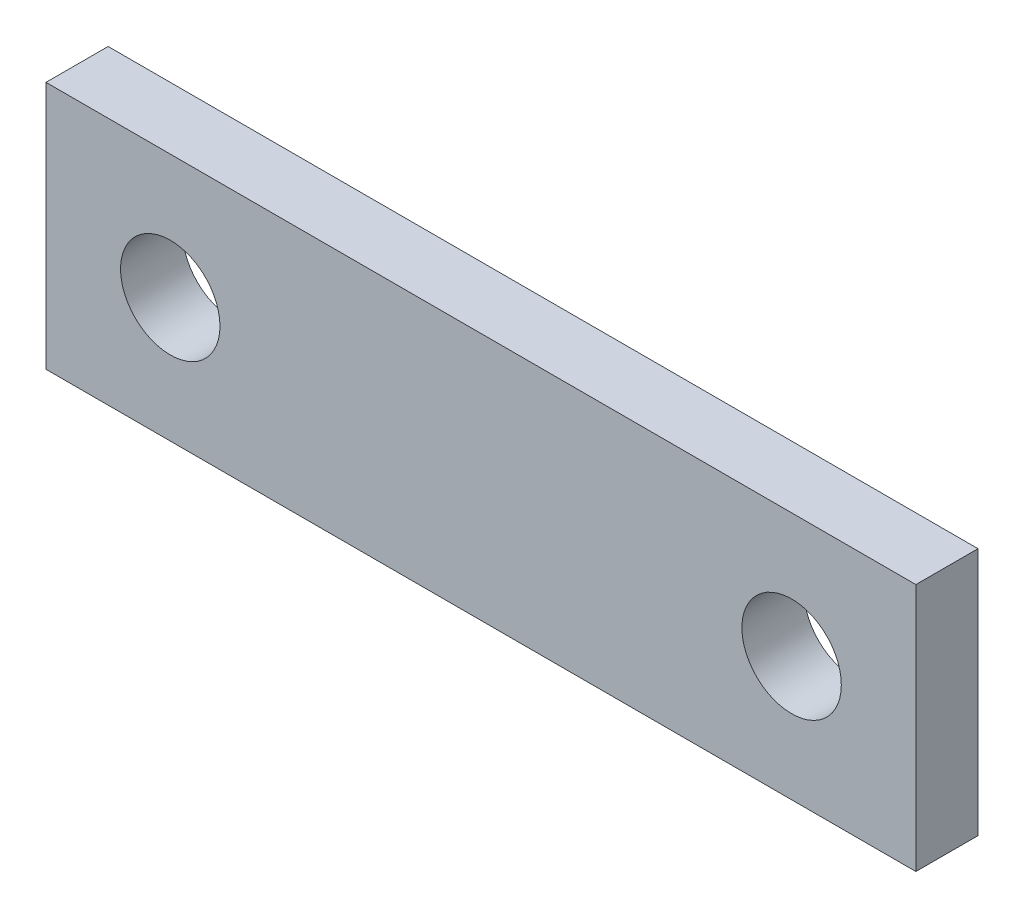
SolidWorks part; units mm, degrees
ref_plane "前视基准面" through (0, 0, 0) normal (0, 0, 1) x (1, 0, 0)
ref_plane "上视基准面" through (0, 0, 0) normal (0, 1, 0) x (1, 0, 0)
ref_plane "右视基准面" through (0, 0, 0) normal (1, 0, 0) x (0, 0, -1)
sketch "草图1" plane through (0, 0, 0) normal (0, 0, 1) x (1, 0, 0)
  line L0 (0, 0) -> (50, 0) construction
  line L1 (10, -10) -> (40, -10)
  line L2 (-10, 10) -> (10, 10)
  line L3 (-10, 10) -> (-10, -10)
  line L4 (-10, -10) -> (10, -10)
  line L6 (-10, 10) -> (10, -10) construction
  line L7 (-10, -10) -> (10, 10) construction
  line L8 (40, 10) -> (60, 10)
  line L10 (40, -10) -> (60, -10)
  line L11 (60, 10) -> (60, -10)
  line L12 (40, 10) -> (60, -10) construction
  line L13 (40, -10) -> (60, 10) construction
  line L14 (10, 10) -> (40, 10)
  circle A0 centre (0, 0) radius 4
  circle A1 centre (50, 0) radius 4
extrude "凸台-拉伸1" add sketch "草图1" along normal blind 5
